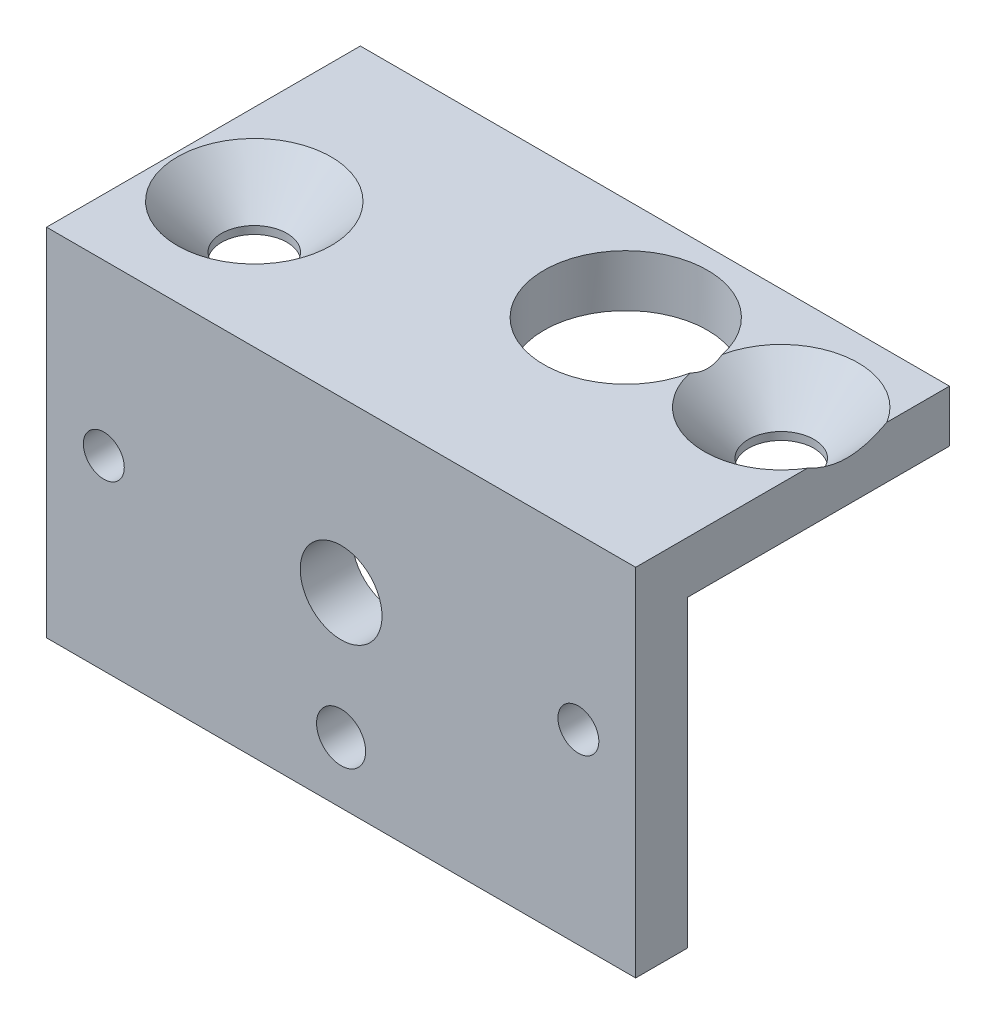
SolidWorks part; units mm, degrees
ref_plane "Front Plane" through (0, 0, 0) normal (0, 0, 1) x (1, 0, 0)
ref_plane "Top Plane" through (0, 0, 0) normal (0, 1, 0) x (1, 0, 0)
ref_plane "Right Plane" through (0, 0, 0) normal (1, 0, 0) x (0, 0, -1)
sketch "Sketch1" plane through (0, 0, 0) normal (0, 0, 1) x (1, 0, 0)
  line L0 (0, 0) -> (0, 2.5277) construction
  line L1 (-18, 12.8677) -> (18, 12.8677)
  line L2 (-18, 12.8677) -> (-18, -8.8677)
  line L3 (0, 0) -> (0, -8.8677) construction
  line L4 (18, 12.8677) -> (18, -8.8677)
  line L7 (18, -8.8677) -> (-18, -8.8677)
  circle A1 centre (-14.5, 2.5277) radius 1.25
  circle A2 centre (14.5, 2.5277) radius 1.25
  circle A3 centre (0, 2.5277) radius 2.5
  circle A4 centre (0, -5.1323) radius 1.5
  point P0 (0, 0)
  dimension "D1" = 14.5
  dimension "D3" = 10.34
  dimension "D4" = 18
  dimension "D2" = 14.5
extrude "Boss-Extrude1" add sketch "Sketch1" along normal blind 3.175
cosmetic thread "Cosmetic Thread1" parameters "D2"=3
cosmetic thread "Cosmetic Thread2" parameters "D2"=3
sketch "Sketch2" plane through (0, 0, 0) normal (0, 0, -1) x (-1, 0, 0)
  line L0 (-18, -8.8677) -> (-18, 12.8677) construction
  line L1 (18, 12.8677) -> (-18, 12.8677)
  line L2 (-18, 12.8677) -> (18, 12.8677) construction
  line L3 (18, 9.6927) -> (-18, 9.6927)
  line L4 (-18, 12.8677) -> (-18, 9.6927)
  line L5 (18, 12.8677) -> (18, -8.8677) construction
  line L8 (-18, -8.8677) -> (-18, 12.8677) construction
  line L9 (18, 12.8677) -> (18, 9.6927)
extrude "Boss-Extrude2" add sketch "Sketch2" along normal blind 16 from surface at 0 starting at face at (2.5, 2.5277, 0)
sketch "Sketch3" plane through (0, 9.6927, 0) normal (0, -1, 0) x (1, 0, 0)
  line L0 (18, -16) -> (18, 0) construction
  circle A0 centre (4.475, -9.7441) radius 5
  circle A1 centre (-13.025, -4.5441) radius 2
  circle A2 centre (13.975, -9.7441) radius 2
  dimension "D2" = 27
  dimension "D3" = 9.5
  dimension "D4" = 13.525
extrude "Cut-Extrude1" cut sketch "Sketch3" against normal blind 10
hole_wizard "Escareado para parafuso de máquina com cabeça chata de M42" positions "Esboço4" profile "Esboço3" countersink size "M4" standard "Métrico Ansi" end condition through all
sketch "Esboço4" plane through (0, 12.8677, 0) normal (0, 1, 0) x (-1, 0, 0)
  point P0 (13.025, -4.5441)
  point P4 (-13.975, -9.7441)
sketch "Esboço3" plane through (-13.025, 12.8677, -4.5441) normal (1, 0, 0) x (0, 0, 1)
  line L0 (0, 0) -> (0, 21.7354)
  line L1 (0, 21.7354) -> (2, 21.7354)
  line L2 (2, 21.7354) -> (2, 2.7)
  line L3 (2, 2.7) -> (4.7, 0)
  line L5 (4.7, 0) -> (0, 0)
  line L6 (-2, 2.7) -> (-4.7, 0) construction
  line L11 (0, -6.35) -> (0, 107.95) construction
  dimension "Thru Hole Dia." = 4
  dimension "Thru Hole Depth" = 21.7354
  dimension "Near C'Sink Dia." = 9.4
  dimension "Near C'Sink Angle" = 90
